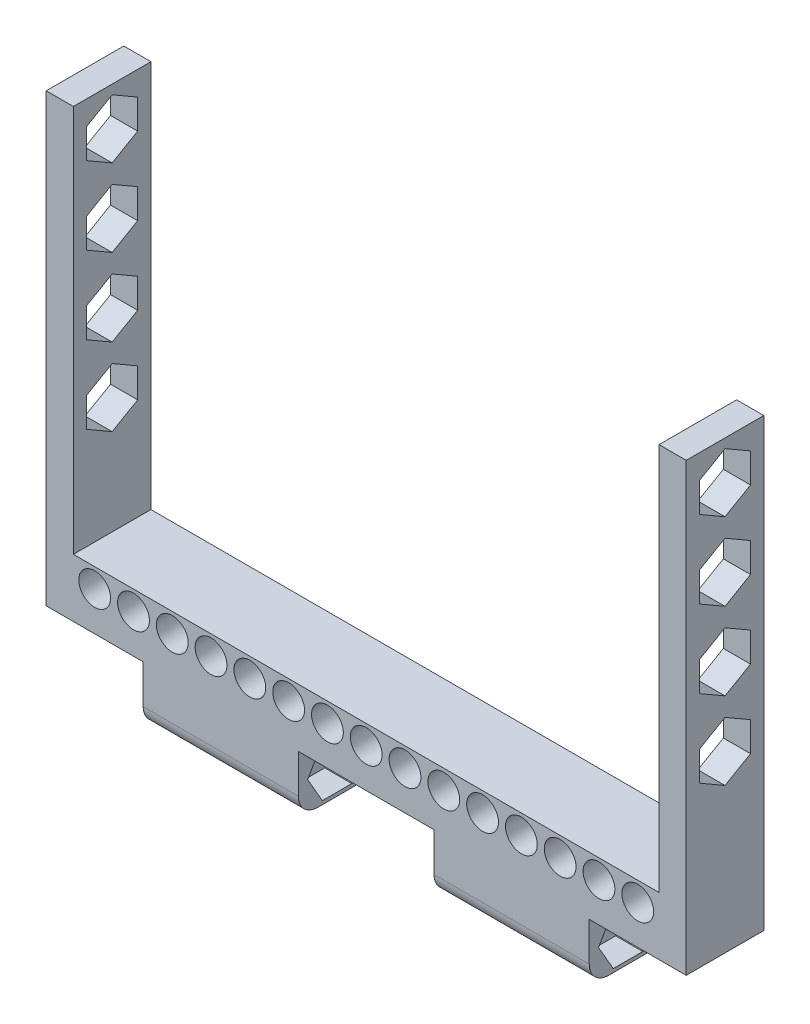
SolidWorks part; units mm, degrees
ref_plane "Front Plane" through (0, 0, 0) normal (0, 0, 1) x (1, 0, 0)
ref_plane "Top Plane" through (0, 0, 0) normal (0, 1, 0) x (1, 0, 0)
ref_plane "Right Plane" through (0, 0, 0) normal (1, 0, 0) x (0, 0, -1)
sketch "Эскиз1" plane through (0, 0, 0) normal (0, 1, 0) x (1, 0, 0)
  line L1 (0, 0) -> (-165, 0)
  line L2 (0, 0) -> (0, -20)
  line L3 (0, -20) -> (-165, -20)
  line L4 (-165, 0) -> (-165, -20)
  dimension "D1" = 165
  dimension "D2" = 20
extrude "Бобышка-Вытянуть1" add sketch "Эскиз1" along normal blind 15
sketch "Эскиз2" plane through (0, 15, 0) normal (0, 1, 0) x (1, 0, 0)
  line L0 (-165, -20) -> (0, -20) construction
  line L1 (-165, 0) -> (-158, 0)
  line L2 (-165, 0) -> (-165, -20)
  line L3 (-165, -20) -> (-158, -20)
  line L4 (-158, 0) -> (-158, -20)
  line L6 (0, 0) -> (-7, 0)
  line L7 (0, 0) -> (0, -20)
  line L8 (0, -20) -> (-7, -20)
  line L9 (-7, 0) -> (-7, -20)
  dimension "D1" = 7
  dimension "D2" = 7
extrude "Бобышка-Вытянуть2" add sketch "Эскиз2" along normal blind 100
sketch "Эскиз3" plane through (0, 0, 20) normal (0, 0, 1) x (1, 0, 0)
  line L0 (-158, 15) -> (-7, 15) construction
  circle A0 centre (-82.5, 10) radius 4.1
  dimension "D1" = 5
extrude "Вырез-Вытянуть1" cut sketch "Эскиз3" against normal through all contours A0
pattern_linear "Линейный массив1" count 8 spacing 10 along (-1, 0, 0) count 8 spacing 10 along (1, 0, 0) of "Вырез-Вытянуть1"
sketch "Эскиз4" plane through (-165, 0, 0) normal (-1, 0, 0) x (0, 0, 1)
  line L0 (0, 115) -> (20, 115) construction
  line L1 (10, 97.4) -> (16.5818, 101.2)
  line L2 (16.5818, 101.2) -> (16.5818, 108.8)
  line L3 (16.5818, 108.8) -> (10, 112.6)
  line L4 (10, 112.6) -> (3.4182, 108.8)
  line L5 (3.4182, 108.8) -> (3.4182, 101.2)
  line L6 (3.4182, 101.2) -> (10, 97.4)
  line L7 (0, 115) -> (0, 0) construction
  circle A0 centre (10, 105) radius 6.5818 construction
  dimension "D1" = 15.2
  dimension "D3" = 10
  dimension "D4" = 10
extrude "Вырез-Вытянуть2" cut sketch "Эскиз4" against normal through all
sketch "Эскиз5" plane through (0, 0, 0) normal (0, -1, 0) x (1, 0, 0)
  line L0 (-165, 20) -> (0, 20) construction
  line L1 (-140, 20) -> (-100, 20)
  line L2 (-140, 20) -> (-140, 0)
  line L3 (-140, 0) -> (-100, 0)
  line L4 (-100, 20) -> (-100, 0)
  line L5 (0, 0) -> (-165, 0) construction
  line L6 (-165, 0) -> (-165, 20) construction
  line L7 (-65, 20) -> (-25, 20)
  line L8 (-65, 20) -> (-65, 0)
  line L9 (-65, 0) -> (-25, 0)
  line L10 (-25, 20) -> (-25, 0)
  line L11 (0, 20) -> (0, 0) construction
  dimension "D1" = 25
  dimension "D2" = 25
  dimension "D3" = 40
  dimension "D4" = 40
extrude "Бобышка-Вытянуть3" add sketch "Эскиз5" along normal blind 15
sketch "Эскиз6" plane through (-140, 0, 0) normal (-1, 0, 0) x (0, 0, 1)
  line L0 (0, -15) -> (0, 0) construction
  line L1 (20, -15) -> (0, -15) construction
  circle A0 centre (10, -7.5) radius 4.2
  dimension "D1" = 10
  dimension "D2" = 8.4
  dimension "D3" = 7.5
extrude "Вырез-Вытянуть4" cut sketch "Эскиз6" against normal through all
sketch "Эскиз7" plane through (-140, 0, 0) normal (-1, 0, 0) x (0, 0, 1)
  line L1 (17.6, -7.5) -> (13.8, -0.9182)
  line L2 (13.8, -0.9182) -> (6.2, -0.9182)
  line L3 (6.2, -0.9182) -> (2.4, -7.5)
  line L4 (2.4, -7.5) -> (6.2, -14.0818)
  line L5 (6.2, -14.0818) -> (13.8, -14.0818)
  line L6 (13.8, -14.0818) -> (17.6, -7.5)
  circle A0 centre (10, -7.5) radius 6.5818 construction
  dimension "D1" = 15.2
extrude "Вырез-Вытянуть5" cut sketch "Эскиз7" against normal blind 7
sketch "Эскиз8" plane through (-100, 0, 0) normal (1, 0, 0) x (0, 0, -1)
  line L1 (-17.6, -7.5) -> (-13.8, -14.0818)
  line L2 (-13.8, -14.0818) -> (-6.2, -14.0818)
  line L3 (-6.2, -14.0818) -> (-2.4, -7.5)
  line L4 (-2.4, -7.5) -> (-6.2, -0.9182)
  line L5 (-6.2, -0.9182) -> (-13.8, -0.9182)
  line L6 (-13.8, -0.9182) -> (-17.6, -7.5)
  circle A0 centre (-10, -7.5) radius 6.5818 construction
  dimension "D1" = 15.2
extrude "Вырез-Вытянуть6" cut sketch "Эскиз8" against normal blind 7
sketch "Эскиз9" plane through (-65, 0, 0) normal (-1, 0, 0) x (0, 0, 1)
  line L1 (17.6, -7.5) -> (13.8, -0.9182)
  line L2 (13.8, -0.9182) -> (6.2, -0.9182)
  line L3 (6.2, -0.9182) -> (2.4, -7.5)
  line L4 (2.4, -7.5) -> (6.2, -14.0818)
  line L5 (6.2, -14.0818) -> (13.8, -14.0818)
  line L6 (13.8, -14.0818) -> (17.6, -7.5)
  circle A0 centre (10, -7.5) radius 6.5818 construction
  dimension "D1" = 15.2
extrude "Вырез-Вытянуть7" cut sketch "Эскиз9" against normal blind 7
sketch "Эскиз10" plane through (-25, 0, 0) normal (1, 0, 0) x (0, 0, -1)
  line L1 (-2.4, -7.5) -> (-6.2, -0.9182)
  line L2 (-6.2, -0.9182) -> (-13.8, -0.9182)
  line L3 (-13.8, -0.9182) -> (-17.6, -7.5)
  line L4 (-17.6, -7.5) -> (-13.8, -14.0818)
  line L5 (-13.8, -14.0818) -> (-6.2, -14.0818)
  line L6 (-6.2, -14.0818) -> (-2.4, -7.5)
  circle A0 centre (-10, -7.5) radius 6.5818 construction
  dimension "D1" = 15.2
extrude "Вырез-Вытянуть8" cut sketch "Эскиз10" against normal blind 7
fillet "Скругление1" radius 5 2 edges at (-45, -15, 0) (-45, -15, 20)
fillet "Скругление2" radius 5 2 edges at (-120, -15, 20) (-120, -15, 0)
pattern_linear "Линейный массив2" count 4 spacing 20 along (0, -1, 0) of "Вырез-Вытянуть2"
